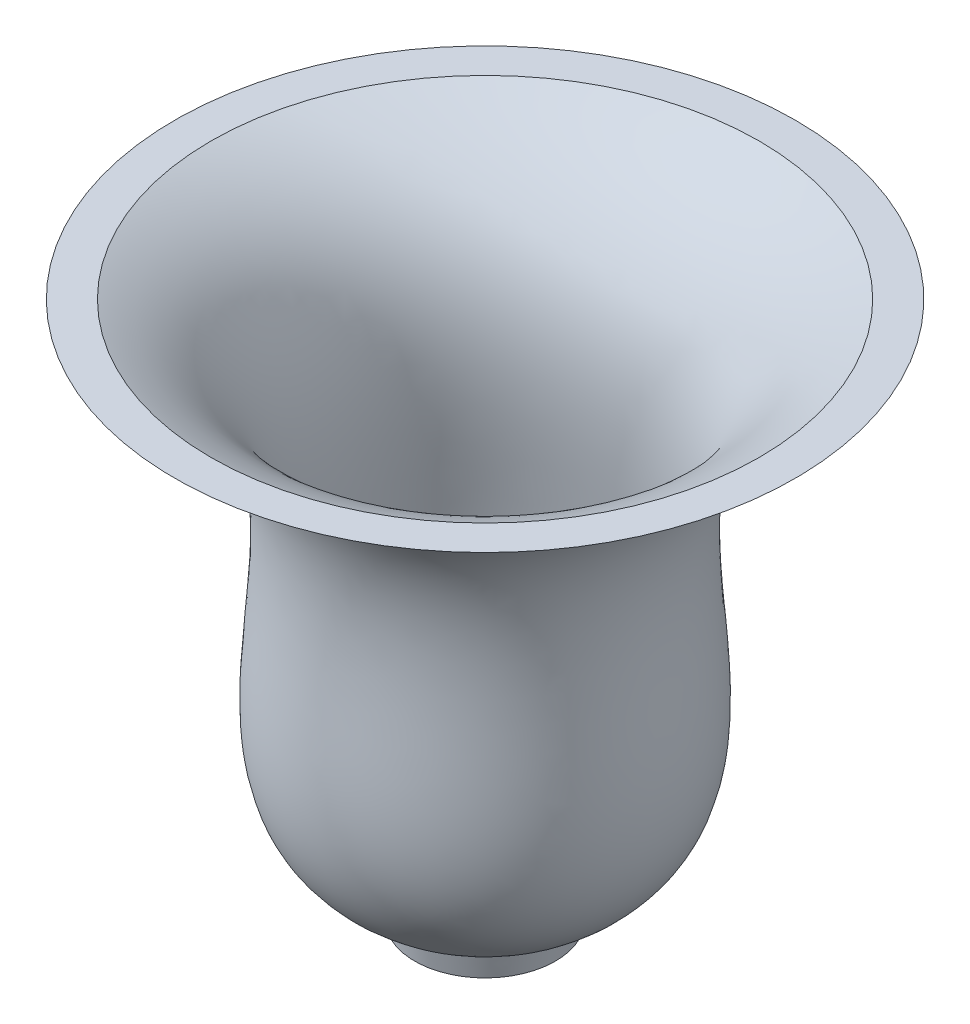
SolidWorks part; units mm, degrees
ref_plane "前视基准面" through (0, 0, 0) normal (0, 0, 1) x (1, 0, 0)
ref_plane "上视基准面" through (0, 0, 0) normal (0, 1, 0) x (1, 0, 0)
ref_plane "右视基准面" through (0, 0, 0) normal (1, 0, 0) x (0, 0, -1)
sketch "草图1" plane through (0, 0, 0) normal (0, 0, 1) x (1, 0, 0)
  line L0 (8.1774, 37.4302) -> (43.1481, 37.4302)
  line L1 (16.6461, -20.2154) -> (8.1774, -20.2154)
  line L2 (8.1774, -20.2154) -> (8.1774, 37.4302)
  spline S0 degree 3 poles (43.1481, 37.4302) (9.5193, 25.9068) (42.9279, -8.5464) (16.6461, -20.2154) knots 0 0 0 0 1 1 1 1
  point P3 (8.1774, -21.6175)
  point P7 (0, 0)
  point P8 (30.795, 25.6729)
  point P9 (26.4611, 15.348)
  point P10 (27.8633, -11.1652)
  point P11 (16.6461, -20.2154)
  point P12 (27.2259, 7.5725)
  point P13 (26.8435, -5.939)
  point P14 (26.8435, -9.1257)
revolve "旋转1" add sketch "草图1" angle 360 about L2
shell "抽壳2" thickness 1.5
sketch "草图2" plane through (0, -20.2154, 0) normal (0, -1, 0) x (1, 0, 0)
  circle A0 centre (8.1774, 0) radius 8.4687
extrude "凸台-拉伸1" add sketch "草图2" along normal blind 3 draft 10
sketch "草图3" plane through (0, -23.2154, 0) normal (0, -1, 0) x (1, 0, 0)
  circle A0 centre (8.1774, 0) radius 7.1248
extrude "切除-拉伸1" cut sketch "草图3" against normal blind 3 draft 10
